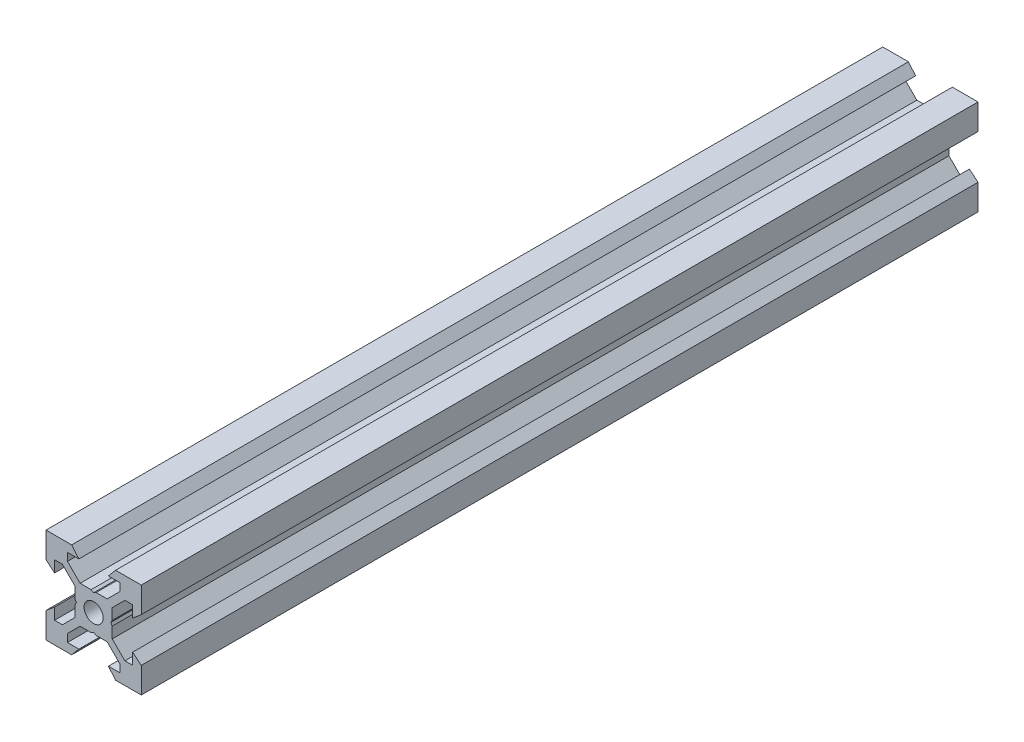
SolidWorks part; units mm, degrees
ref_plane "Front Plane" through (0, 0, 0) normal (0, 0, 1) x (1, 0, 0)
ref_plane "Top Plane" through (0, 0, 0) normal (0, 1, 0) x (1, 0, 0)
ref_plane "Right Plane" through (0, 0, 0) normal (1, 0, 0) x (0, 0, -1)
sketch "Sketch1" plane through (0, 0, 0) normal (0, 0, 1) x (1, 0, 0)
  line L0 (10, 10) -> (4.6104, 10) construction
  line L1 (10, 10) -> (10, 4.6104) construction
  line L2 (10, -10) -> (10, -4.6104) construction
  line L3 (10, -10) -> (4.6104, -10) construction
  line L4 (10, 10) -> (10, 4.6104)
  line L5 (6.5607, 5.5) -> (8.2, 5.5)
  line L6 (5.5, 8.2) -> (5.5, 6.5607)
  line L7 (10, 10) -> (4.6104, 10)
  line L8 (10, 10) -> (10, 4.6104)
  line L9 (6.5607, 5.5) -> (3.9, 2.8393)
  line L10 (5.5, 6.5607) -> (2.8393, 3.9)
  line L11 (10, 4.6104) -> (8.2, 3.1)
  line L12 (4.6104, 10) -> (3.1, 8.2)
  line L13 (8.2, 3.1) -> (8.2, 5.5)
  line L14 (3.1, 8.2) -> (5.5, 8.2)
  line L15 (-6.5607, 5.5) -> (-8.2, 5.5)
  line L16 (6.5607, -5.5) -> (8.2, -5.5)
  line L17 (3.1, -8.2) -> (5.5, -8.2)
  line L18 (8.2, -3.1) -> (8.2, -5.5)
  line L19 (4.6104, -10) -> (3.1, -8.2)
  line L20 (10, -4.6104) -> (8.2, -3.1)
  line L21 (0.5196, -3.9) -> (0, -3.6)
  line L22 (0.5196, 3.9) -> (0, 3.6)
  line L23 (3.6, 0) -> (3.9, -0.5196)
  line L24 (3.9, 0.5196) -> (3.6, 0)
  line L25 (3.9, 0.5196) -> (3.9, 2.8393)
  line L26 (2.8393, 3.9) -> (0.5196, 3.9)
  line L27 (3.9, -2.8393) -> (3.9, -0.5196)
  line L28 (2.8393, -3.9) -> (0.5196, -3.9)
  line L29 (5.5, -6.5607) -> (2.8393, -3.9)
  line L30 (6.5607, -5.5) -> (3.9, -2.8393)
  line L31 (10, -10) -> (10, -4.6104)
  line L32 (10, -10) -> (4.6104, -10)
  line L33 (5.5, -8.2) -> (5.5, -6.5607)
  line L34 (-6.5607, -5.5) -> (-8.2, -5.5)
  line L35 (10, -10) -> (10, -4.6104)
  line L36 (0, 0) -> (0, 8.2) construction
  line L37 (-10, -10) -> (-4.6104, -10) construction
  line L38 (-10, -10) -> (-10, -4.6104) construction
  line L39 (-10, 10) -> (-10, 4.6104) construction
  line L40 (-10, 10) -> (-4.6104, 10) construction
  line L41 (-10, -10) -> (-10, -4.6104)
  line L43 (-5.5, -8.2) -> (-5.5, -6.5607)
  line L44 (-10, -10) -> (-4.6104, -10)
  line L45 (-10, -10) -> (-10, -4.6104)
  line L46 (-6.5607, -5.5) -> (-3.9, -2.8393)
  line L47 (-5.5, -6.5607) -> (-2.8393, -3.9)
  line L48 (-2.8393, -3.9) -> (-0.5196, -3.9)
  line L49 (-3.9, -2.8393) -> (-3.9, -0.5196)
  line L50 (-2.8393, 3.9) -> (-0.5196, 3.9)
  line L51 (-3.9, 0.5196) -> (-3.9, 2.8393)
  line L52 (-3.9, 0.5196) -> (-3.6, 0)
  line L53 (-3.6, 0) -> (-3.9, -0.5196)
  line L54 (-0.5196, 3.9) -> (0, 3.6)
  line L55 (-0.5196, -3.9) -> (0, -3.6)
  line L56 (-10, -4.6104) -> (-8.2, -3.1)
  line L57 (-4.6104, -10) -> (-3.1, -8.2)
  line L58 (-8.2, -3.1) -> (-8.2, -5.5)
  line L59 (-3.1, -8.2) -> (-5.5, -8.2)
  line L60 (-10, -10) -> (10, -10) construction
  line L61 (-10, -10) -> (-10, 10) construction
  line L62 (-3.1, 8.2) -> (-5.5, 8.2)
  line L63 (-8.2, 3.1) -> (-8.2, 5.5)
  line L64 (-4.6104, 10) -> (-3.1, 8.2)
  line L65 (-10, 4.6104) -> (-8.2, 3.1)
  line L66 (-5.5, 6.5607) -> (-2.8393, 3.9)
  line L67 (-6.5607, 5.5) -> (-3.9, 2.8393)
  line L68 (-10, 10) -> (-10, 4.6104)
  line L69 (-10, 10) -> (-4.6104, 10)
  line L70 (-5.5, 8.2) -> (-5.5, 6.5607)
  line L71 (-10, 10) -> (10, 10) construction
  line L72 (-10, 10) -> (-10, 4.6104)
  line L73 (10, -10) -> (10, 10) construction
  line L74 (-10, -10) -> (10, 10) construction
  line L75 (-10, 10) -> (10, -10) construction
  circle A0 centre (0, 0) radius 2
  dimension "D7" = 4
  dimension "D1" = 20
  dimension "D2" = 5.3896
  dimension "D3" = 4.5
  dimension "D4" = 50
  dimension "D5" = 1.8
  dimension "D6" = 1.5104
  dimension "D8" = 5.5
  dimension "D9" = 120
  dimension "D10" = 0.3
  dimension "D11" = 2.3197
  dimension "D12" = 7.8
  dimension "D13" = 7.8
  dimension "D14" = 1.5
  dimension "D15" = 2.6607
extrude "Boss-Extrude1" add sketch "Sketch1" along normal mid plane 175.69 contours L70 L62 L64 L69 L68 L65 L63 L15 L67 L51 L52 L53 L49 L46 L34 L58 L56 L41 L44 L57 L59 L43 L47 L48 L55 L21 L28 L29 L33 L17 L19 L32 L31 L20 L18 L16 L30 L27 L23 L24 L25 L9 L5 L13 L11 L4 L7 L12 L14 L6 L10
